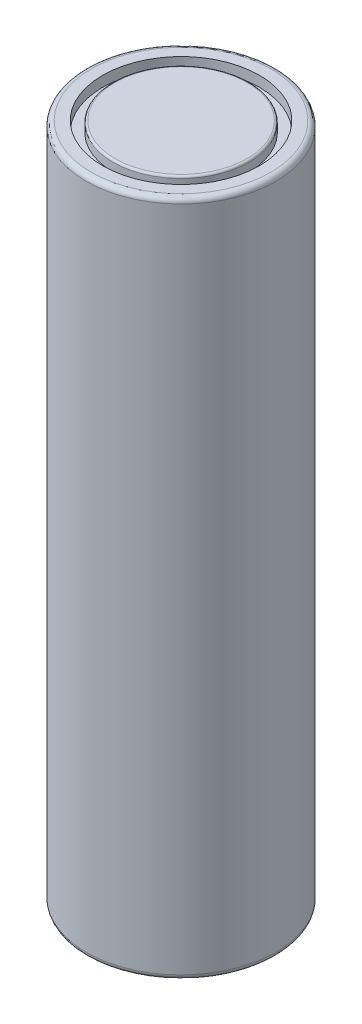
SolidWorks part; units mm, degrees
ref_plane "Front Plane" through (0, 0, 0) normal (0, 0, 1) x (1, 0, 0)
ref_plane "Top Plane" through (0, 0, 0) normal (0, 1, 0) x (1, 0, 0)
ref_plane "Right Plane" through (0, 0, 0) normal (1, 0, 0) x (0, 0, -1)
sketch "Sketch1" plane through (0, 0, 0) normal (0, 1, 0) x (1, 0, 0)
  circle A0 centre (0, 0) radius 9.1
  dimension "D1" = 18.2
extrude "Boss-Extrude1" add sketch "Sketch1" along normal blind 65
sketch "Sketch2" plane through (0, 65, 0) normal (0, 1, 0) x (1, 0, 0)
  circle A0 centre (0, 0) radius 7.5158
  circle A1 centre (0, 0) radius 6.5281
extrude "Cut-Extrude1" cut sketch "Sketch2" against normal blind 1 contours A0
fillet "Fillet1" radius 0.5 2 edges at (0, 0, 9.1) (0, 65, 9.1)
sketch "Sketch3" plane through (0, 0, 0) normal (0, -1, 0) x (1, 0, 0)
  circle A0 centre (0, 0) radius 7.5158
  circle A1 centre (0, 0) radius 6.5281
extrude "Cut-Extrude2" cut sketch "Sketch3" against normal blind 1
fillet "Fillet2" radius 0.2 2 edges at (0, 0, -6.5281) (0, 65, 6.5281)
